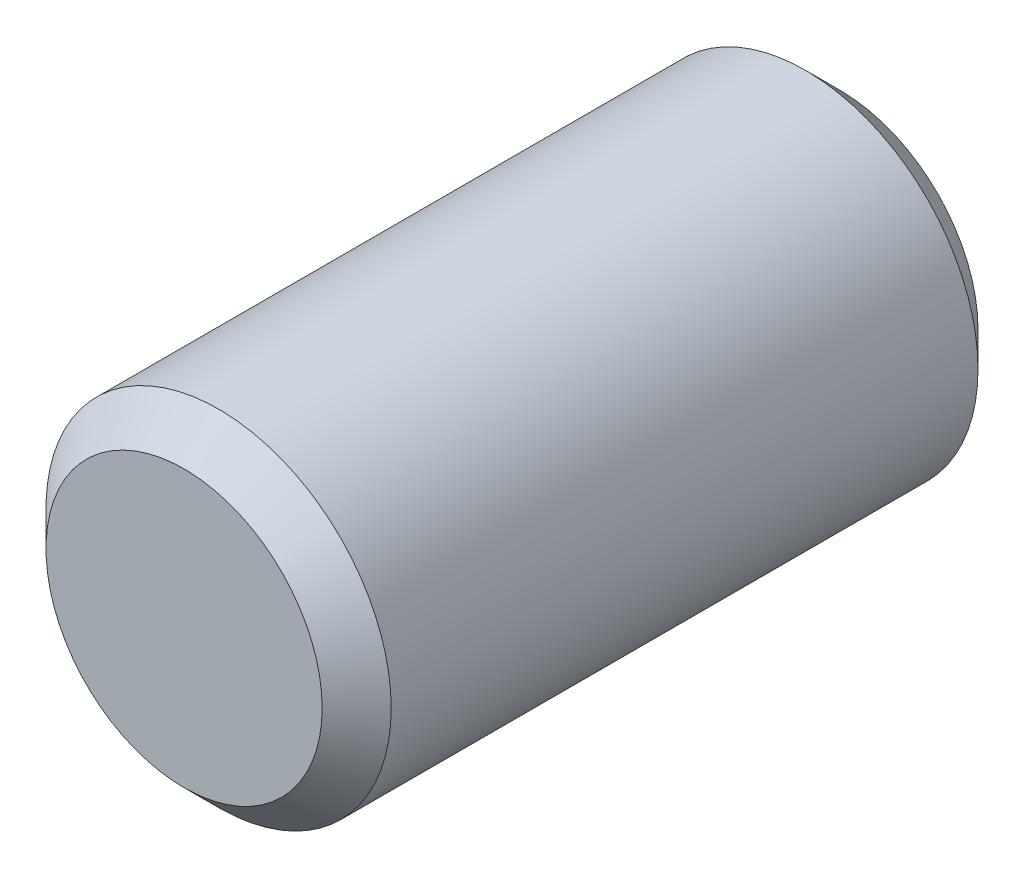
SolidWorks part; units mm, degrees
ref_plane "Plan de face" through (0, 0, 0) normal (0, 0, 1) x (1, 0, 0)
ref_plane "Plan de dessus" through (0, 0, 0) normal (0, 1, 0) x (1, 0, 0)
ref_plane "Plan de droite" through (0, 0, 0) normal (1, 0, 0) x (0, 0, -1)
sketch "Esquisse1" plane through (0, 0, 0) normal (0, 0, 1) x (1, 0, 0)
  circle A0 centre (0, 0) radius 50
extrude "Boss.-Extru.1" add sketch "Esquisse1" along normal blind 190
chamfer "Chanfrein2" distance 10 angle 45 2 edges at (50, 0, 0) (50, 0, 190)
